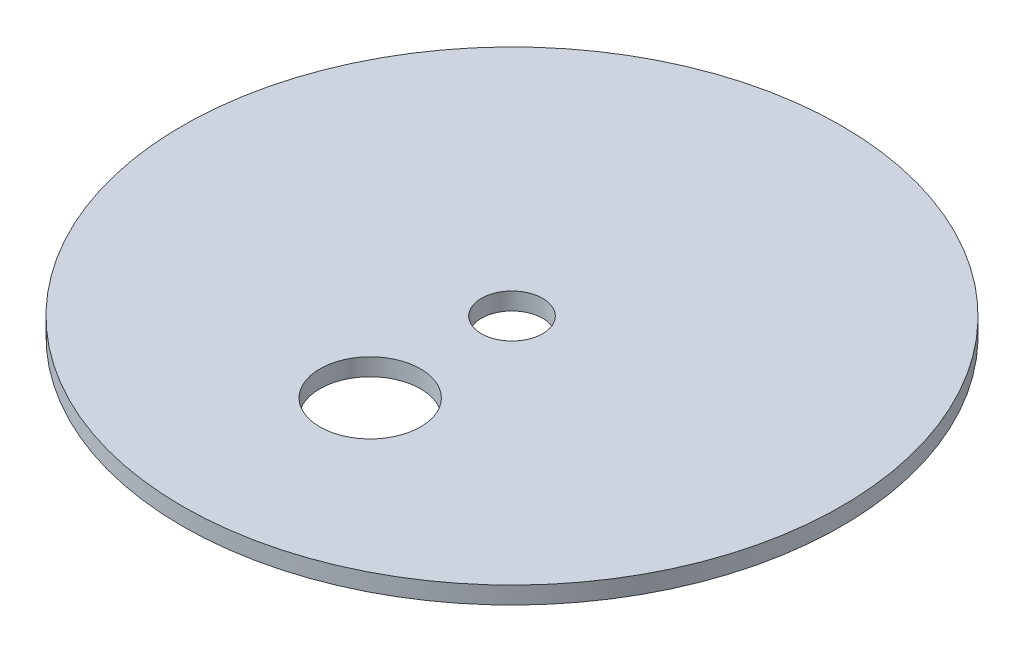
SolidWorks part; units mm, degrees
material "PVC Rigid"
ref_plane "Front" through (0, 0, 0) normal (0, 0, 1) x (1, 0, 0)
ref_plane "Top" through (0, 0, 0) normal (0, 1, 0) x (1, 0, 0)
ref_plane "Right" through (0, 0, 0) normal (1, 0, 0) x (0, 0, -1)
sketch "Sketch1" plane through (0, 0, 0) normal (0, 1, 0) x (1, 0, 0)
  circle A0 centre (0, 0) radius 57.15
  dimension "D1" = 114.3
extrude "Boss-Extrude1" add sketch "Sketch1" along normal blind 3
sketch "Sketch2" plane through (0, 0, 0) normal (0, 1, 0) x (1, 0, 0)
  circle A0 centre (0, 0) radius 5.3155
  circle A1 centre (0, -24.5888) radius 8.7297
extrude "Cut-Extrude2" cut sketch "Sketch2" against normal blind 3 and the other way blind 13
